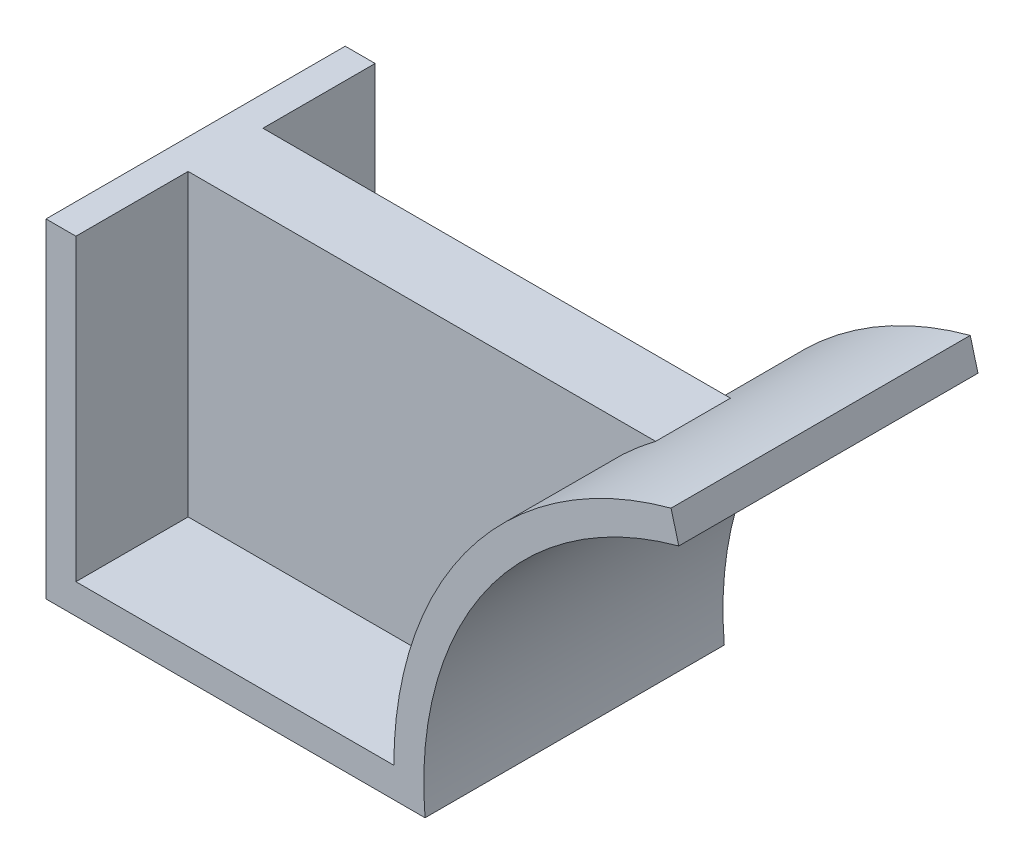
SolidWorks part; units mm, degrees
ref_plane "Front Plane" through (0, 0, 0) normal (0, 0, 1) x (1, 0, 0)
ref_plane "Top Plane" through (0, 0, 0) normal (0, 1, 0) x (1, 0, 0)
ref_plane "Right Plane" through (0, 0, 0) normal (1, 0, 0) x (0, 0, -1)
sketch "Sketch1" plane through (0, 0, 0) normal (0, 0, 1) x (1, 0, 0)
  line L0 (0, 80) -> (0, 0)
  line L1 (0, 0) -> (85, 0)
  line L2 (85, 0) -> (185, 0) construction
  line L3 (185, 0) -> (141.9318, 160.7327) construction
  arc A0 (85, 0) -> (159.1181, 96.5926) centre (185, 0) cw
  point P6 (0, 0)
  dimension "D3" = 100
  dimension "D1" = 80
  dimension "D2" = 85
  dimension "D4" = 75
extrude "Extrude-Thin1" add sketch "Sketch1" along normal blind 80 thin
sketch "Sketch2" plane through (0, 0, 0) normal (1, 0, 0) x (0, 0, -1)
  line L0 (-80, 0) -> (0, 0) construction
  line L5 (-50, 0) -> (-30, 0)
  line L6 (-50, 0) -> (-50, 80)
  line L7 (-50, 80) -> (-30, 80)
  line L8 (-30, 0) -> (-30, 80)
  line L9 (-80, 80) -> (0, 80) construction
  point P0 (-41.7605, 27.7918)
  point P10 (-40, 80)
  dimension "D1" = 20
extrude "Boss-Extrude1" add sketch "Sketch2" along normal up to surface (85 mm away)
